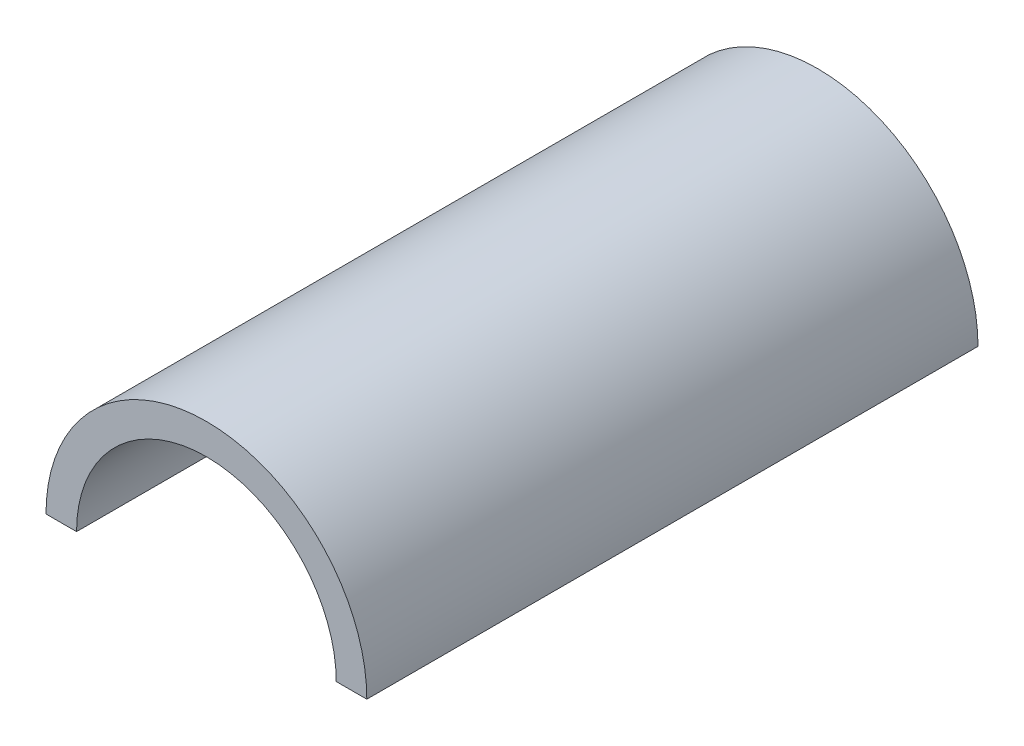
SolidWorks part; units mm, degrees
ref_plane "Front" through (0, 0, 0) normal (0, 0, 1) x (1, 0, 0)
ref_plane "Top" through (0, 0, 0) normal (0, 1, 0) x (1, 0, 0)
ref_plane "Right" through (0, 0, 0) normal (1, 0, 0) x (0, 0, -1)
sketch "Sketch1" plane through (0, 0, 0) normal (0, 0, 1) x (1, 0, 0)
  line L0 (-37.5443, 7.712) -> (-44.5293, 7.712)
  line L1 (21.8155, 7.712) -> (28.8005, 7.712)
  arc A0 (-37.5443, 7.712) -> (21.8155, 7.712) centre (-7.8644, 7.712) cw
  arc A1 (-44.5293, 7.712) -> (28.8005, 7.712) centre (-7.8644, 7.712) cw
extrude "Boss-Extrude1" add sketch "Sketch1" along normal blind 139.7
sketch "Sketch2" plane through (0, 7.712, 0) normal (0, -1, 0) x (-1, 0, 0)
  line L0 (41.0368, -139.7) -> (41.0368, -76.2)
  line L1 (44.5293, -139.7) -> (37.5443, -139.7) construction
  line L2 (-25.308, -139.7) -> (-25.308, -76.2)
  line L3 (-21.8155, -139.7) -> (-28.8005, -139.7) construction
hole_wizard "1/8 (0.125) Diameter Hole1" positions "Sketch5" profile "Sketch4" hole size "1/8" standard "ANSI Inch"
sketch "Sketch5" plane through (0, 7.712, 0) normal (0, -1, 0) x (-1, 0, 0)
  point P0 (41.0368, -76.2)
  point P3 (-25.308, -76.2)
sketch "Sketch4" plane through (-41.0368, 7.712, 76.2) normal (1, 0, 0) x (0, 0, -1)
  line L0 (0, 0) -> (0, 1.4539)
  line L1 (0, 1.4539) -> (1.5875, 0.5)
  line L2 (1.5875, 0.5) -> (1.5875, 0)
  line L5 (1.5875, 0) -> (0, 0)
  line L10 (0, 1.4539) -> (-1.5875, 0.5) construction
  line L11 (0, -6.35) -> (0, 107.95) construction
  dimension "Hole Dia." = 3.175
  dimension "Hole Depth" = 0.5
  dimension "Drill Angle" = 118
pattern_linear "LPattern1" count 5 spacing 11.43 along (0, 0, -1) of "1/8 (0.125) Diameter Hole1"
